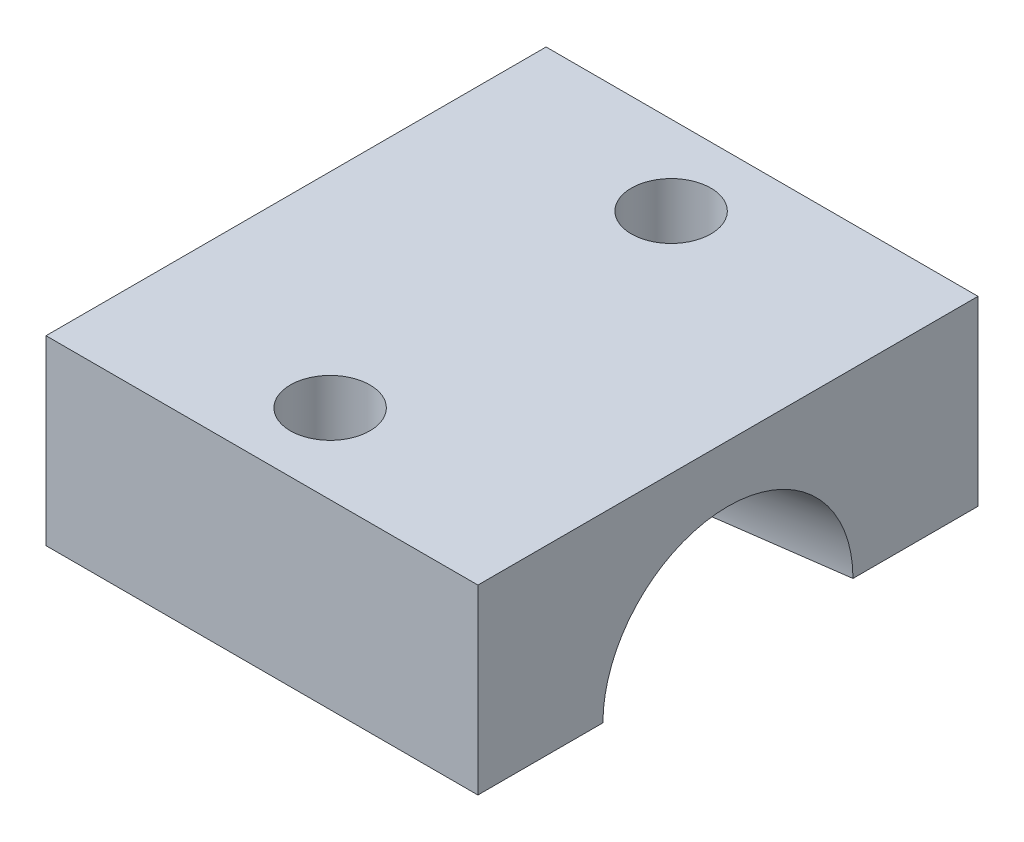
SolidWorks part; units mm, degrees
ref_plane "前基準面" through (0, 0, 0) normal (0, 0, 1) x (1, 0, 0)
ref_plane "上基準面" through (0, 0, 0) normal (0, 1, 0) x (1, 0, 0)
ref_plane "右基準面" through (0, 0, 0) normal (1, 0, 0) x (0, 0, -1)
sketch "草圖1" plane through (0, 0, 0) normal (0, 1, 0) x (1, 0, 0)
  line L0 (-3.5728, 0) -> (5.6377, 0) construction
  line L1 (-8.5, -11) -> (8.5, -11)
  line L2 (-8.5, -11) -> (-8.5, 11)
  line L3 (-8.5, 11) -> (8.5, 11)
  line L4 (8.5, -11) -> (8.5, 11)
  line L5 (-8.5, -11) -> (8.5, 11) construction
  line L6 (-8.5, 11) -> (8.5, -11) construction
  circle A1 centre (-1.5, 7.5) radius 1.75
  circle A2 centre (-1.5, -7.5) radius 1.75
  point P0 (0, 0)
  dimension "D3" = 3.5
  dimension "D4" = 3.5
  dimension "D5" = 7
  dimension "D1" = 22
  dimension "D2" = 17
extrude "填料-伸長1" add sketch "草圖1" along normal mid plane 8
sketch "草圖2" plane through (-8.5, 0, 0) normal (-1, 0, 0) x (0, 0, 1)
  line L0 (-11, -4) -> (11, -4) construction
  circle A0 centre (0, -4) radius 3.5
  dimension "D1" = 7
extrude "除料-伸長1" cut sketch "草圖2" against normal blind 2.5 contours A0
sketch "草圖3" plane through (-6, 0, 0) normal (-1, 0, 0) x (0, 0, 1)
  line L0 (3.5, -4) -> (-3.5, -4) construction
  circle A0 centre (0, -4) radius 3.5
  dimension "D1" = 7
sketch "草圖4" plane through (8.5, 0, 0) normal (1, 0, 0) x (0, 0, -1)
  circle A0 centre (0, -4) radius 5.5
  dimension "D1" = 11
loft "除料-疊層拉伸1" cut profiles "草圖4", "草圖3"
sketch "草圖5" plane through (-8.5, 0, 0) normal (-1, 0, 0) x (0, 0, 1)
  line L0 (3.5, -4) -> (11, -4)
  line L1 (-11, 4) -> (11, 4)
  line L2 (-11, 4) -> (-11, -4)
  line L3 (-11, -4) -> (-3.5, -4)
  line L4 (11, 4) -> (11, -4)
  arc A0 (3.5, -4) -> (-3.5, -4) centre (0, -4) ccw
  arc A1 (3.5, -4) -> (-3.5, -4) centre (0, -4) ccw construction
  point P15 (0, 0)
extrude "填料-伸長2" add sketch "草圖5" along normal blind 2
